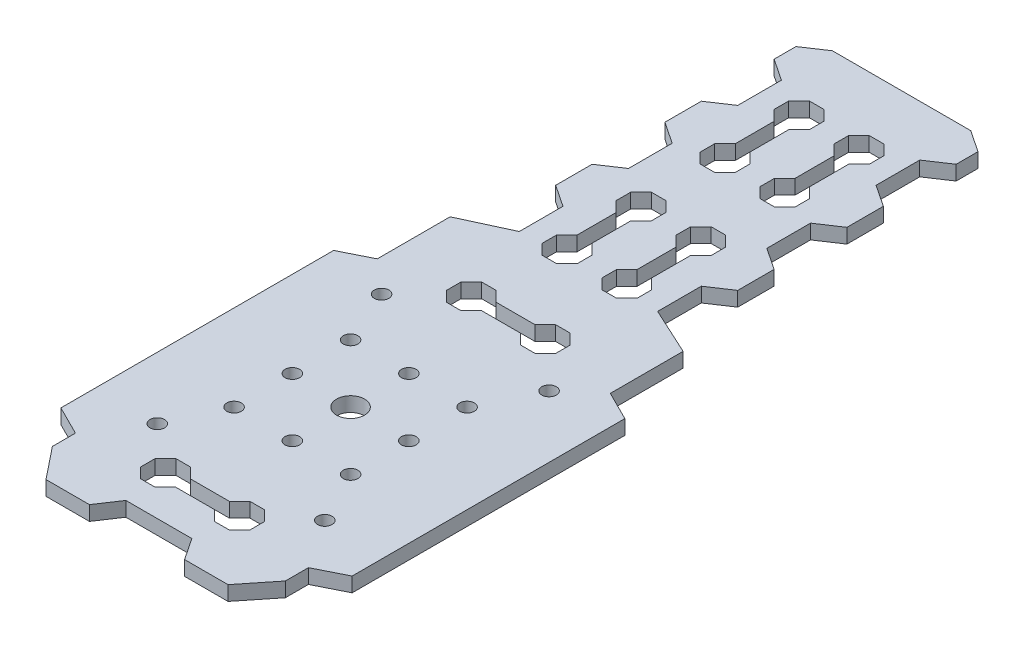
SolidWorks part; units mm, degrees
ref_plane "Front Plane" through (0, 0, 0) normal (0, 0, 1) x (1, 0, 0)
ref_plane "Top Plane" through (0, 0, 0) normal (0, 1, 0) x (1, 0, 0)
ref_plane "Right Plane" through (0, 0, 0) normal (1, 0, 0) x (0, 0, -1)
sketch "Sketch1" plane through (0, 0, 0) normal (0, 1, 0) x (1, 0, 0)
  line L0 (0, 0) -> (4.5326, 0)
  line L3 (16, 1.376) -> (16, 4.5439)
  line L4 (16, 4.5439) -> (20, 6.5439)
  line L5 (20, 6.5439) -> (20, 44)
  line L6 (20, 44) -> (16, 46)
  line L7 (16, 46) -> (16, 56)
  line L8 (16, 56) -> (9.5, 59)
  line L9 (9.5, 59) -> (9.5, 65)
  line L10 (9.5, 65) -> (12.5, 67)
  line L11 (12.5, 67) -> (12.5, 72)
  line L12 (12.5, 72) -> (9.5, 74)
  line L13 (9.5, 74) -> (9.5, 80)
  line L14 (9.5, 80) -> (12.5, 82)
  line L15 (12.5, 82) -> (12.5, 87)
  line L16 (12.5, 87) -> (9.5, 89)
  line L17 (9.5, 89) -> (9.5, 95)
  line L18 (9.5, 95) -> (12.5, 97)
  line L19 (12.5, 97) -> (12.5, 100)
  line L20 (12.5, 100) -> (9.5, 102)
  line L21 (9.5, 102) -> (0, 102)
  line L22 (0, 102) -> (0, 49)
  line L23 (6.5326, -3) -> (12.5, -3)
  line L24 (12.5, -3) -> (16, 1.376)
  line L25 (4.5326, 0) -> (6.5326, -3)
  line L26 (9.5, 89) -> (9.5, 80) construction
  line L27 (9.5, 74) -> (9.5, 65) construction
  line L28 (12.5, 97) -> (12.5, 87) construction
  line L29 (12.5, 82) -> (12.5, 72) construction
  line L30 (16, 46) -> (16, 4.5439) construction
  line L31 (9.5, 95) -> (9.5, 102) construction
  line L32 (3.1116, 94.4467) -> (5.1116, 94.4467)
  line L33 (5.1116, 94.4467) -> (6.5259, 93.0325)
  line L34 (6.5259, 93.0325) -> (6.5259, 91.0325)
  line L35 (6.5259, 91.0325) -> (5.1116, 89.6183)
  line L36 (5.1116, 89.6183) -> (5.1116, 84.2751)
  line L37 (5.1116, 84.2751) -> (6.5259, 82.8609)
  line L38 (6.5259, 82.8609) -> (6.5259, 80.8609)
  line L39 (6.5259, 80.8609) -> (5.1116, 79.4467)
  line L40 (5.1116, 79.4467) -> (3.1116, 79.4467)
  line L41 (3.1116, 79.4467) -> (1.6974, 80.8609)
  line L42 (1.6974, 80.8609) -> (1.6974, 82.8609)
  line L43 (1.6974, 82.8609) -> (3.1116, 84.2751)
  line L44 (3.1116, 84.2751) -> (3.1116, 89.6183)
  line L45 (3.1116, 89.6183) -> (1.6974, 91.0325)
  line L46 (1.6974, 91.0325) -> (1.6974, 93.0325)
  line L47 (1.6974, 93.0325) -> (3.1116, 94.4467)
  line L48 (3.1116, 89.6183) -> (5.1116, 89.6183) construction
  line L49 (3.1116, 84.2751) -> (5.1116, 84.2751) construction
  line L50 (3.1116, 72.7442) -> (5.1116, 72.7442)
  line L51 (5.1116, 72.7442) -> (6.5259, 71.33)
  line L52 (6.5259, 71.33) -> (6.5259, 69.33)
  line L53 (6.5259, 69.33) -> (5.1116, 67.9157)
  line L54 (5.1116, 67.9157) -> (5.1116, 62.5726)
  line L55 (5.1116, 62.5726) -> (6.5259, 61.1584)
  line L56 (6.5259, 61.1584) -> (6.5259, 59.1584)
  line L57 (6.5259, 59.1584) -> (5.1116, 57.7442)
  line L58 (5.1116, 57.7442) -> (3.1116, 57.7442)
  line L59 (3.1116, 57.7442) -> (1.6974, 59.1584)
  line L60 (1.6974, 59.1584) -> (1.6974, 61.1584)
  line L61 (1.6974, 61.1584) -> (3.1116, 62.5726)
  line L62 (3.1116, 62.5726) -> (3.1116, 67.9157)
  line L63 (3.1116, 67.9157) -> (1.6974, 69.33)
  line L64 (1.6974, 69.33) -> (1.6974, 71.33)
  line L65 (1.6974, 71.33) -> (3.1116, 72.7442)
  line L66 (3.1116, 67.9157) -> (5.1116, 67.9157) construction
  line L67 (3.1116, 62.5726) -> (5.1116, 62.5726) construction
  line L68 (3.1116, 79.4467) -> (3.1116, 72.7442) construction
  line L69 (7.5, 49) -> (7.5, 47)
  line L70 (7.5, 47) -> (6.0858, 45.5858)
  line L71 (6.0858, 45.5858) -> (4.0858, 45.5858)
  line L72 (4.0858, 45.5858) -> (2.6716, 47)
  line L73 (2.6716, 47) -> (0, 47)
  line L81 (0, 49) -> (2.6716, 49)
  line L82 (2.6716, 49) -> (4.0858, 50.4142)
  line L83 (4.0858, 50.4142) -> (6.0858, 50.4142)
  line L84 (6.0858, 50.4142) -> (7.5, 49)
  line L85 (2.6716, 49) -> (2.6716, 47) construction
  line L86 (0, 47) -> (0, 7)
  line L87 (7.5, 7) -> (7.5, 5)
  line L88 (7.5, 5) -> (6.0858, 3.5858)
  line L89 (6.0858, 3.5858) -> (4.0858, 3.5858)
  line L90 (4.0858, 3.5858) -> (2.6716, 5)
  line L91 (2.6716, 5) -> (0, 5)
  line L92 (0, 7) -> (2.6716, 7)
  line L93 (2.6716, 7) -> (4.0858, 8.4142)
  line L94 (4.0858, 8.4142) -> (6.0858, 8.4142)
  line L95 (6.0858, 8.4142) -> (7.5, 7)
  line L96 (2.6716, 7) -> (2.6716, 5) construction
  line L97 (0, 5) -> (0, 0)
  dimension "D1" = 105
  dimension "D3" = 3
  dimension "D4" = 6
  dimension "D5" = 5
  dimension "D6" = 6
  dimension "D7" = 5
  dimension "D8" = 6
  dimension "D9" = 2
  dimension "D10" = 3
  dimension "D11" = 2
  dimension "D12" = 2
  dimension "D13" = 2
  dimension "D14" = 3
  dimension "D15" = 3
  dimension "D16" = 2
  dimension "D17" = 12.5
  dimension "D18" = 2
  dimension "D19" = 10
  dimension "D20" = 2
  dimension "D21" = 2
  dimension "D22" = 2
  dimension "D23" = 20
  dimension "D24" = 16
  dimension "D25" = 2
  dimension "D26" = 2
  dimension "D27" = 2
  dimension "D28" = 2
  dimension "D29" = 2
  dimension "D30" = 2
  dimension "D31" = 2
  dimension "D32" = 2
  dimension "D33" = 2
  dimension "D34" = 2
  dimension "D35" = 2
  dimension "D36" = 2
  dimension "D37" = 2
  dimension "D38" = 2
  dimension "D39" = 45
  dimension "D40" = 45
  dimension "D41" = 45
  dimension "D42" = 45
  dimension "D43" = 45
  dimension "D44" = 2
  dimension "D45" = 15
  dimension "D46" = 2
  dimension "D47" = 2
  dimension "D48" = 2
  dimension "D49" = 2
  dimension "D50" = 2
  dimension "D51" = 2
  dimension "D52" = 2
  dimension "D53" = 2
  dimension "D54" = 2
  dimension "D55" = 2
  dimension "D56" = 2
  dimension "D57" = 2
  dimension "D58" = 2
  dimension "D59" = 2
  dimension "D60" = 45
  dimension "D61" = 45
  dimension "D62" = 45
  dimension "D63" = 45
  dimension "D64" = 45
  dimension "D65" = 2
  dimension "D66" = 15
  dimension "D67" = 2
  dimension "D68" = 2
  dimension "D69" = 2
  dimension "D70" = 2
  dimension "D71" = 2
  dimension "D72" = 2
  dimension "D73" = 2
  dimension "D74" = 7.5
  dimension "D75" = 2
  dimension "D76" = 2
  dimension "D77" = 2
  dimension "D78" = 2
  dimension "D79" = 2
  dimension "D80" = 2
  dimension "D81" = 2
  dimension "D82" = 45
  dimension "D83" = 45
  dimension "D84" = 45
  dimension "D85" = 45
  dimension "D86" = 2
  dimension "D87" = 2
  dimension "D88" = 2
  dimension "D89" = 7.5
  dimension "D90" = 40
  dimension "D91" = 5
extrude "Boss-Extrude1" add sketch "Sketch1" along normal blind 2
mirror "Mirror1" about plane through (0, 0, 0) normal (1, 0, 0) of "Boss-Extrude1"
sketch "Sketch2" plane through (0, 2, 0) normal (0, 1, 0) x (1, 0, 0)
  line L0 (-8.1996, 18.5298) -> (7.8004, 18.5298) construction
  line L1 (7.8004, 18.5298) -> (7.8004, 34.5298) construction
  line L2 (7.8004, 34.5298) -> (-8.1996, 34.5298) construction
  line L3 (-8.1996, 34.5298) -> (-8.1996, 18.5298) construction
  line L4 (-0.1996, 34.5298) -> (-0.1996, 18.5298) construction
  line L5 (-8.1996, 26.5298) -> (7.8004, 26.5298) construction
  line L6 (-0.1996, 18.5298) -> (0, 0) construction
  line L7 (-11.5, 42.089) -> (11.5, 42.089) construction
  line L8 (11.5, 42.089) -> (11.5, 11.2851) construction
  line L9 (11.5, 11.2851) -> (-11.5, 11.2851) construction
  line L10 (-11.5, 11.2851) -> (-11.5, 42.089) construction
  line L11 (0, 11.2851) -> (0, 0) construction
  circle A0 centre (-0.1996, 26.5298) radius 1.9205
  circle A1 centre (-8.1996, 34.5298) radius 1
  circle A2 centre (-0.1996, 34.5298) radius 1
  circle A3 centre (7.8004, 34.5298) radius 1
  circle A4 centre (7.8004, 26.5298) radius 1
  circle A5 centre (7.8004, 18.5298) radius 1
  circle A6 centre (-0.1996, 18.5298) radius 1
  circle A7 centre (-8.1996, 18.5298) radius 1
  circle A8 centre (-8.1996, 26.5298) radius 1
  circle A9 centre (-11.5, 42.089) radius 1
  circle A10 centre (11.5, 42.089) radius 1
  circle A11 centre (11.5, 11.2851) radius 1
  circle A12 centre (-11.5, 11.2851) radius 1
  point P8 (-0.1996, 26.5298)
  dimension "D1" = 16
  dimension "D2" = 16
  dimension "D3" = 23
extrude "Cut-Extrude1" cut sketch "Sketch2" against normal blind 10
